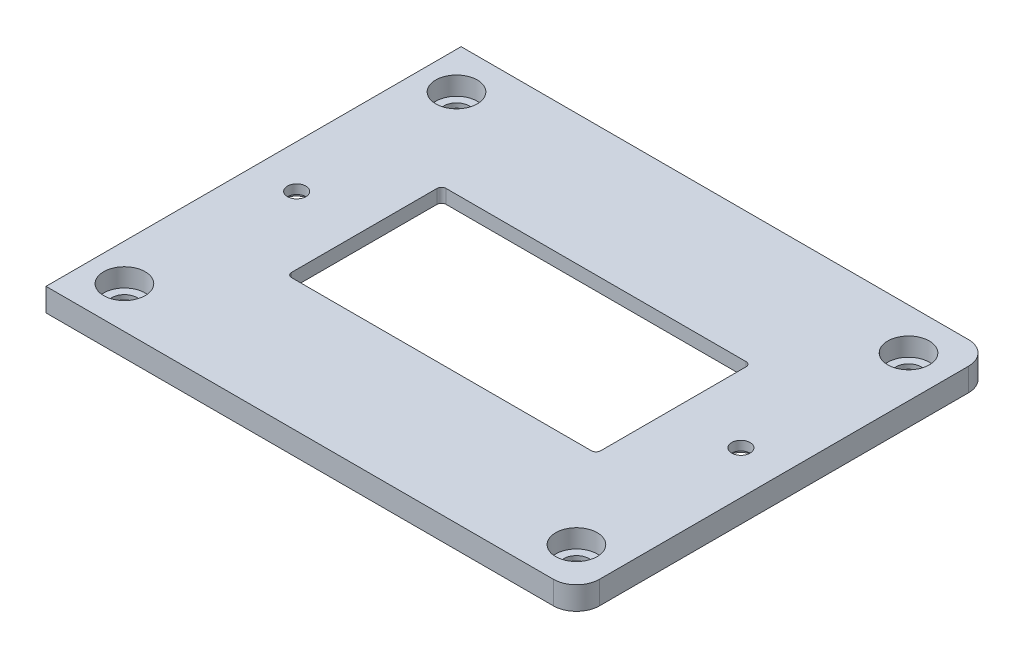
SolidWorks part; units mm, degrees
ref_plane "Front Plane" through (0, 0, 0) normal (0, 0, 1) x (1, 0, 0)
ref_plane "Top Plane" through (0, 0, 0) normal (0, 1, 0) x (1, 0, 0)
ref_plane "Right Plane" through (0, 0, 0) normal (1, 0, 0) x (0, 0, -1)
sketch "Sketch1" plane through (0, 0, 0) normal (0, 1, 0) x (1, 0, 0)
  line L0 (-48.15, 0) -> (48.15, 0)
  line L1 (-57.5, -45) -> (57.5, -45)
  line L2 (-57.5, -45) -> (-57.5, 45)
  line L3 (-57.5, 45) -> (57.5, 45)
  line L4 (57.5, -45) -> (57.5, 45)
  line L5 (-57.5, -45) -> (57.5, 45) construction
  line L6 (-57.5, 45) -> (57.5, -45) construction
  line L7 (-33.5, -16.75) -> (33.5, -16.75)
  line L8 (-33.5, -16.75) -> (-33.5, 16.75)
  line L9 (-33.5, 16.75) -> (33.5, 16.75)
  line L10 (33.5, -16.75) -> (33.5, 16.75)
  line L11 (-33.5, -16.75) -> (33.5, 16.75) construction
  line L12 (-33.5, 16.75) -> (33.5, -16.75) construction
  point P0 (0, 0)
  point P6 (0, 0)
  point P14 (0, 0)
  dimension "D1" = 90
  dimension "D2" = 115
  dimension "D3" = 67
  dimension "D4" = 33.5
  dimension "D5" = 96.3
extrude "Boss-Extrude1" add sketch "Sketch1" along normal blind 5
fillet "Fillet1" radius 5 2 edges at (57.5, 2.5, 45) (57.5, 2.5, -45)
fillet "Fillet2" radius 1 4 edges at (-33.5, 2.5, 16.75) (33.5, 2.5, 16.75) (-33.5, 2.5, -16.75) (33.5, 2.5, -16.75)
hole_wizard "CBORE for M5 SHCS1" positions "Sketch2" profile "Sketch4" counterbore size "M5" standard "ANSI Metric" end condition through all
sketch "Sketch2" plane through (0, 5, 0) normal (0, 1, 0) x (1, 0, 0)
  line L1 (-57.5, 40) -> (52.5, 40)
  line L2 (-57.5, 40) -> (-57.5, -40)
  line L3 (-57.5, -40) -> (52.5, -40)
  line L4 (52.5, 40) -> (52.5, -40)
  line L5 (-57.5, -45) -> (-57.5, 45) construction
  line L6 (-57.5, 45) -> (52.5, 45) construction
  line L7 (57.5, -40) -> (57.5, 40) construction
  line L8 (-57.5, -45) -> (52.5, -45) construction
  point P0 (-49.5, 36)
  point P2 (-49.5, -36)
  point P4 (48.5, -36)
  point P6 (48.5, 36)
  dimension "D1" = 5
  dimension "D2" = 5
  dimension "D3" = 5
  dimension "D4" = 8
  dimension "D5" = 4
  dimension "D6" = 4
  dimension "D7" = 4
sketch "Sketch4" plane through (-49.5, 5, -36) normal (1, 0, 0) x (0, 0, 1)
  line L0 (0, 0) -> (0, 5)
  line L1 (0, 5) -> (2.75, 5)
  line L3 (2.75, 5) -> (2.75, 4)
  line L4 (2.75, 4) -> (4.5, 4)
  line L5 (4.5, 4) -> (4.5, 0)
  line L7 (4.5, 0) -> (0, 0)
  line L11 (0, -6.35) -> (0, 107.95) construction
  dimension "Thru Hole Dia." = 5.5
  dimension "Thru Hole Depth" = 5
  dimension "C'Bore Dia." = 9
  dimension "C'Bore Depth" = 4
sketch "Sketch5" plane through (0, 0, 0) normal (0, -1, 0) x (1, 0, 0)
  line L0 (-57.5, 45) -> (-57.5, -45) construction
  line L1 (-57.5, 30) -> (53.5, 30)
  line L2 (-57.5, 30) -> (-57.5, -30)
  line L3 (-57.5, -30) -> (53.5, -30)
  line L4 (53.5, 30) -> (53.5, -30)
  line L5 (57.5, 40) -> (57.5, -40) construction
  line L6 (-57.5, 45) -> (52.5, 45) construction
  line L7 (-57.5, -45) -> (52.5, -45) construction
  dimension "D1" = 4
  dimension "D2" = 15
  dimension "D3" = 15
extrude "Cut-Extrude1" cut sketch "Sketch5" against normal blind 2
hole_wizard "CBORE for M5 SHCS2" positions "Sketch6" profile "Sketch7" counterbore size "M5" standard "ANSI Metric" end condition through all
sketch "Sketch6" plane through (0, 2, 0) normal (0, -1, 0) x (-1, 0, 0)
  line L0 (48.15, 0) -> (-48.15, 0)
  line L2 (57.5, -30) -> (57.5, 30) construction
  line L3 (-32.5, 16.75) -> (32.5, 16.75) construction
  point P0 (48.15, 0)
  point P1 (-48.15, 0)
  point P8 (57.5, 0)
  point P12 (0, 16.75)
  point P13 (0, 0)
  dimension "D1" = 96.3
sketch "Sketch7" plane through (-48.15, 2, 0) normal (1, 0, 0) x (0, 0, -1)
  line L0 (0, 0) -> (0, 3)
  line L1 (0, 3) -> (2, 3)
  line L3 (2, 3) -> (2, 1)
  line L4 (2, 1) -> (3, 1)
  line L5 (3, 1) -> (3, 0)
  line L7 (3, 0) -> (0, 0)
  line L11 (0, -6.35) -> (0, 107.95) construction
  dimension "Thru Hole Dia." = 4
  dimension "Thru Hole Depth" = 3
  dimension "C'Bore Dia." = 6
  dimension "C'Bore Depth" = 1
